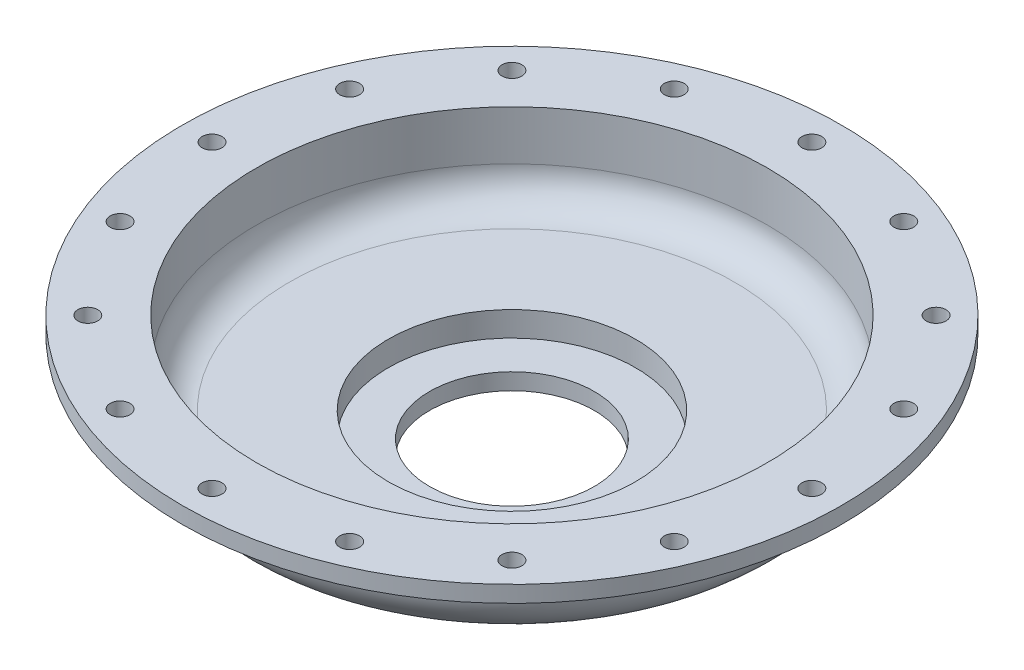
SolidWorks part; units mm, degrees
material "Brass"
ref_plane "Front Plane" through (0, 0, 0) normal (0, 0, 1) x (1, 0, 0)
ref_plane "Top Plane" through (0, 0, 0) normal (0, 1, 0) x (1, 0, 0)
ref_plane "Right Plane" through (0, 0, 0) normal (1, 0, 0) x (0, 0, -1)
sketch "Sketch2" plane through (0, 0, 0) normal (0, 1, 0) x (1, 0, 0)
  circle A0 centre (0, 0) radius 50
  circle A1 centre (0, 0) radius 85
  circle A2 centre (0, 0) radius 165
  circle A3 centre (0, 0) radius 200
  circle A4 centre (0, 0) radius 182 construction
  circle A5 centre (0, 182) radius 6
  dimension "D1" = 100
  dimension "D2" = 170
  dimension "D3" = 330
  dimension "D4" = 400
  dimension "D5" = 364
  dimension "D6" = 12
extrude "Boss-Extrude2" add sketch "Sketch2" along normal blind 75 contours A0
sketch "Sketch3" plane through (0, 75, 0) normal (0, 1, 0) x (1, 0, 0)
  circle A0 centre (0, 0) radius 200
  circle A1 centre (0, 0) radius 165
  circle A3 centre (0, 0) radius 182 construction
  circle A4 centre (0, 182) radius 6
  circle A5 centre (69.6484, 168.1461) radius 6
  circle A6 centre (128.6934, 128.6934) radius 6
  circle A7 centre (168.1461, 69.6484) radius 6
  circle A8 centre (182, 0) radius 6
  circle A9 centre (168.1461, -69.6484) radius 6
  circle A10 centre (128.6934, -128.6934) radius 6
  circle A11 centre (69.6484, -168.1461) radius 6
  circle A12 centre (0, -182) radius 6
  circle A13 centre (-69.6484, -168.1461) radius 6
  circle A14 centre (-128.6934, -128.6934) radius 6
  circle A15 centre (-168.1461, -69.6484) radius 6
  circle A16 centre (-182, 0) radius 6
  circle A17 centre (-168.1461, 69.6484) radius 6
  circle A18 centre (-128.6934, 128.6934) radius 6
  circle A19 centre (-69.6484, 168.1461) radius 6
  point P40 (0, 0)
  dimension "D1" = 400
  dimension "D2" = 330
  dimension "D3" = 12
  dimension "D4" = 16
extrude "Boss-Extrude8" add sketch "Sketch3" against normal blind 10 separate body
sketch "Sketch8" plane through (0, 75, 0) normal (0, 1, 0) x (1, 0, 0)
  circle A0 centre (0, 0) radius 165
extrude "Boss-Extrude9" add sketch "Sketch8" against normal blind 60
fillet "Fillet2" radius 30 1 edges at (0, 15, 165)
sketch "Sketch12" plane through (0, 15, 0) normal (0, -1, 0) x (1, 0, 0)
  circle A0 centre (0, 0) radius 85
  dimension "D1" = 170
extrude "Boss-Extrude11" add sketch "Sketch12" along normal blind 15
sketch "Sketch13" plane through (0, 0, 0) normal (0, -1, 0) x (1, 0, 0)
  circle A0 centre (0, 0) radius 50
  dimension "D1" = 100
extrude "Cut-Extrude4" cut sketch "Sketch13" against normal through all both and the other way through all contours A0
shell "Shell12" thickness 10
sketch "Sketch14" plane through (0, 75, 0) normal (0, 1, 0) x (1, 0, 0)
  circle A0 centre (0, 0) radius 165
  dimension "D1" = 330
sketch "Sketch15" plane through (0, 75, 0) normal (0, 1, 0) x (1, 0, 0)
  circle A0 centre (0, 0) radius 155
  dimension "D1" = 310
extrude "Cut-Extrude7" cut sketch "Sketch15" against normal blind 10
